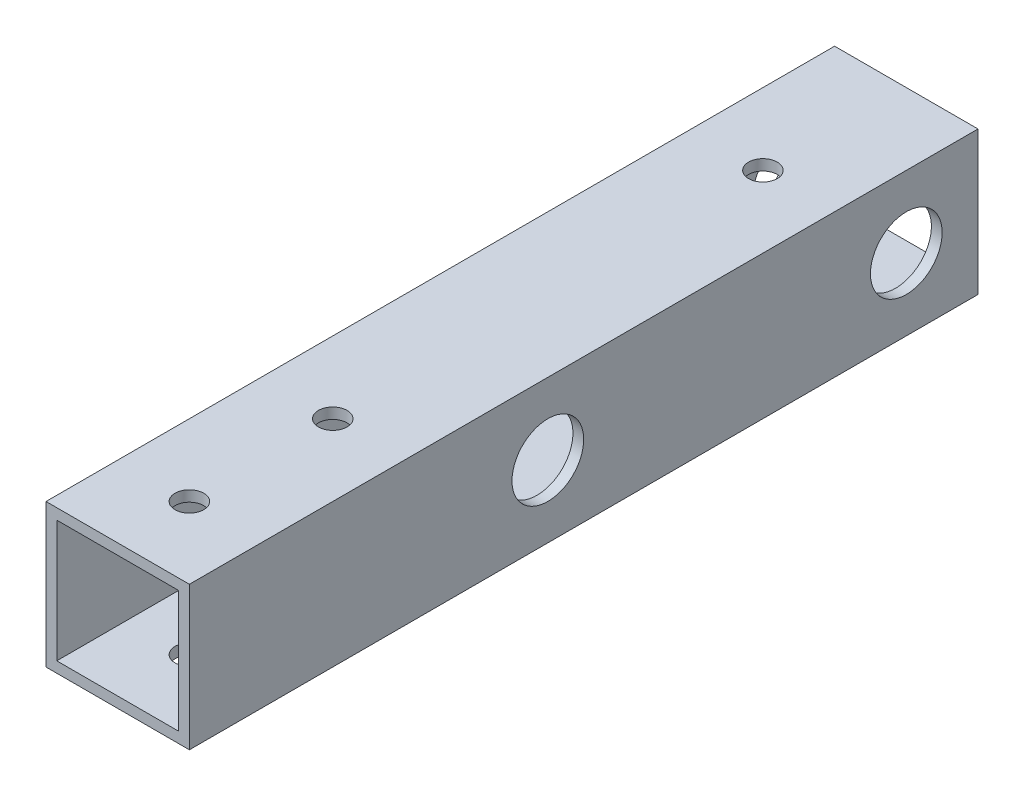
SolidWorks part; units mm, degrees
material "1060 合金"
ref_plane "正面" through (0, 0, 0) normal (0, 0, 1) x (1, 0, 0)
ref_plane "平面" through (0, 0, 0) normal (0, 1, 0) x (1, 0, 0)
ref_plane "右側面" through (0, 0, 0) normal (1, 0, 0) x (0, 0, -1)
sketch "ｽｹｯﾁ1" plane through (0, 0, 0) normal (0, 0, 1) x (1, 0, 0)
  line L1 (-10, -10) -> (10, -10)
  line L2 (-10, -10) -> (-10, 10)
  line L3 (-10, 10) -> (10, 10)
  line L4 (10, -10) -> (10, 10)
  line L5 (-10, -10) -> (10, 10) construction
  line L6 (-10, 10) -> (10, -10) construction
  line L7 (-8.5, -8.5) -> (8.5, -8.5)
  line L8 (-8.5, -8.5) -> (-8.5, 8.5)
  line L9 (-8.5, 8.5) -> (8.5, 8.5)
  line L10 (8.5, -8.5) -> (8.5, 8.5)
  line L11 (-8.5, -8.5) -> (8.5, 8.5) construction
  line L12 (-8.5, 8.5) -> (8.5, -8.5) construction
  point P0 (0, 0)
  point P6 (0, 0)
  dimension "D1" = 1.5
  dimension "D2" = 20
  dimension "D3" = 20
extrude "ﾎﾞｽ - 押し出し1" add sketch "ｽｹｯﾁ1" along normal blind 110
sketch "ｽｹｯﾁ2" plane through (10, 0, 0) normal (1, 0, 0) x (0, 0, -1)
  line L0 (-110, -10) -> (0, -10) construction
  circle A9 centre (-60, 0) radius 2.7
  circle A10 centre (-10, 0) radius 2.7
  dimension "D1" = 50
  dimension "D6" = 5.4
  dimension "D8" = 5.4
  dimension "D4" = 10
  dimension "D5" = 10
  dimension "D9" = 10
extrude "ｶｯﾄ - 押し出し1" cut sketch "ｽｹｯﾁ2" against normal blind 25
sketch "ｽｹｯﾁ3" plane through (0, 10, 0) normal (0, 1, 0) x (1, 0, 0)
  line L0 (10, -110) -> (-10, -110) construction
  line L1 (-10, -110) -> (-10, 0) construction
  circle A0 centre (0, -100) radius 2
  circle A4 centre (0, -80) radius 2
  circle A5 centre (0, -20) radius 2
  dimension "D1" = 4
  dimension "D2" = 10
  dimension "D3" = 10
  dimension "D6" = 2
  dimension "D7" = 20
  dimension "D5" = 20
  dimension "D4" = 2
extrude "ｶｯﾄ - 押し出し2" cut sketch "ｽｹｯﾁ3" against normal blind 20
sketch "ｽｹｯﾁ5" plane through (0, -10, 0) normal (0, -1, 0) x (-1, 0, 0)
  circle A0 centre (0, -20) radius 5
  dimension "D1" = 10
extrude "ｶｯﾄ - 押し出し4" cut sketch "ｽｹｯﾁ5" against normal blind 10
sketch "ｽｹｯﾁ6" plane through (-10, 0, 0) normal (-1, 0, 0) x (0, 0, 1)
  circle A0 centre (10, 0) radius 5
  circle A1 centre (60, 0) radius 5
  dimension "D1" = 10
  dimension "D2" = 10
extrude "ｶｯﾄ - 押し出し5" cut sketch "ｽｹｯﾁ6" against normal blind 10 from offset 10
